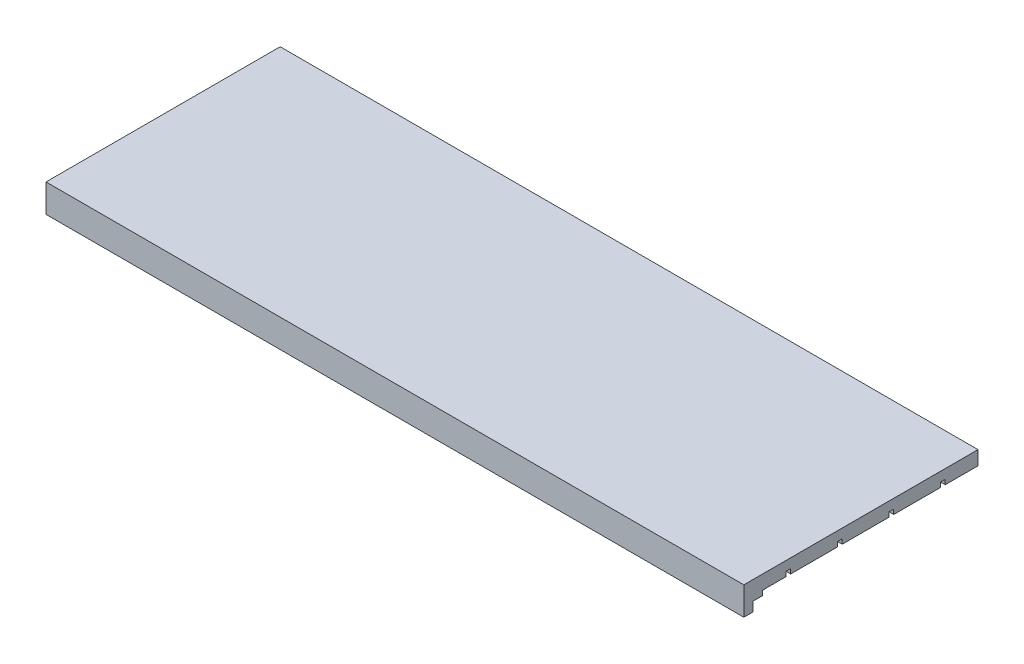
SolidWorks part; units mm, degrees
ref_plane "Front Plane" through (0, 0, 0) normal (0, 0, 1) x (1, 0, 0)
ref_plane "Top Plane" through (0, 0, 0) normal (0, 1, 0) x (1, 0, 0)
ref_plane "Right Plane" through (0, 0, 0) normal (1, 0, 0) x (0, 0, -1)
sketch "Sketch1" plane through (0, 0, 0) normal (0, 1, 0) x (1, 0, 0)
  line L1 (-74.5, 25) -> (74.5, 25)
  line L2 (-74.5, 25) -> (-74.5, -25)
  line L3 (-74.5, -25) -> (74.5, -25)
  line L4 (74.5, 25) -> (74.5, -25)
  line L5 (-74.5, 25) -> (74.5, -25) construction
  line L6 (-74.5, -25) -> (74.5, 25) construction
  point P0 (0, 0)
  dimension "D1" = 149
  dimension "D2" = 50
extrude "Boss-Extrude1" add sketch "Sketch1" along normal blind 3
sketch "Sketch2" plane through (0, 0, 0) normal (0, -1, 0) x (1, 0, 0)
  line L0 (-74.5, -25) -> (-74.5, 25) construction
  line L1 (-74.5, -17) -> (74.5, -17)
  line L2 (-74.5, -17) -> (-74.5, -18)
  line L3 (-74.5, -18) -> (74.5, -18)
  line L4 (74.5, -17) -> (74.5, -18)
  line L5 (74.5, 25) -> (74.5, -25) construction
  line L6 (74.5, -25) -> (-74.5, -25) construction
  line L8 (-74.5, -6) -> (74.5, -6)
  line L9 (-74.5, -6) -> (-74.5, -7)
  line L10 (-74.5, -7) -> (74.5, -7)
  line L11 (74.5, -6) -> (74.5, -7)
  line L12 (-74.5, 5) -> (74.5, 5)
  line L13 (-74.5, 5) -> (-74.5, 4)
  line L14 (-74.5, 4) -> (74.5, 4)
  line L15 (74.5, 5) -> (74.5, 4)
  line L16 (-74.5, 16) -> (74.5, 16)
  line L17 (-74.5, 16) -> (-74.5, 15)
  line L18 (-74.5, 15) -> (74.5, 15)
  line L19 (74.5, 16) -> (74.5, 15)
  dimension "D1" = 1
  dimension "D2" = 7
  dimension "D3" = 1
  dimension "D4" = 10
  dimension "D5" = 1
  dimension "D6" = 10
  dimension "D7" = 1
  dimension "D8" = 10
extrude "Cut-Extrude1" cut sketch "Sketch2" against normal blind 1
sketch "Sketch3" plane through (0, 0, 0) normal (0, -1, 0) x (1, 0, 0)
  line L0 (74.5, 25) -> (74.5, 16) construction
  line L1 (-74.5, 25) -> (74.5, 25)
  line L2 (-74.5, 25) -> (-74.5, 21)
  line L3 (-74.5, 21) -> (74.5, 21)
  line L4 (74.5, 25) -> (74.5, 21)
  dimension "D1" = 4
extrude "Boss-Extrude2" add sketch "Sketch3" along normal blind 1
sketch "Sketch4" plane through (0, -1, 0) normal (0, -1, 0) x (1, 0, 0)
  line L0 (74.5, 21) -> (74.5, 25) construction
  line L1 (-74.5, 25) -> (74.5, 25)
  line L2 (-74.5, 25) -> (-74.5, 23)
  line L3 (-74.5, 23) -> (74.5, 23)
  line L4 (74.5, 25) -> (74.5, 23)
  dimension "D1" = 2
extrude "Boss-Extrude3" add sketch "Sketch4" along normal blind 2
sketch "Sketch5" plane through (0, 0, 0) normal (0, -1, 0) x (1, 0, 0)
  line L0 (74.5, -25) -> (-74.5, -25) construction
  line L1 (-50.5, 23.3339) -> (-46.5, 23.3339)
  line L2 (-50.5, 23.3339) -> (-50.5, -25)
  line L3 (-50.5, -25) -> (-46.5, -25)
  line L4 (-46.5, 23.3339) -> (-46.5, -25)
  line L5 (-74.5, -25) -> (-74.5, -18) construction
  line L6 (0, 21) -> (0, -25) construction
  line L7 (-74.5, 21) -> (74.5, 21) construction
  line L8 (50.5, -25) -> (46.5, -25)
  line L9 (-16.5, 21) -> (-12.5, 21)
  line L10 (-16.5, 21) -> (-16.5, -25)
  line L11 (-16.5, -25) -> (-12.5, -25)
  line L12 (-12.5, 21) -> (-12.5, -25)
  line L13 (46.5, 23.3339) -> (46.5, -25)
  line L14 (50.5, 23.3339) -> (46.5, 23.3339)
  line L15 (50.5, 23.3339) -> (50.5, -25)
  line L16 (16.5, -25) -> (12.5, -25)
  dimension "D1" = 4
  dimension "D2" = 24
  dimension "D3" = 4
  dimension "D4" = 30
